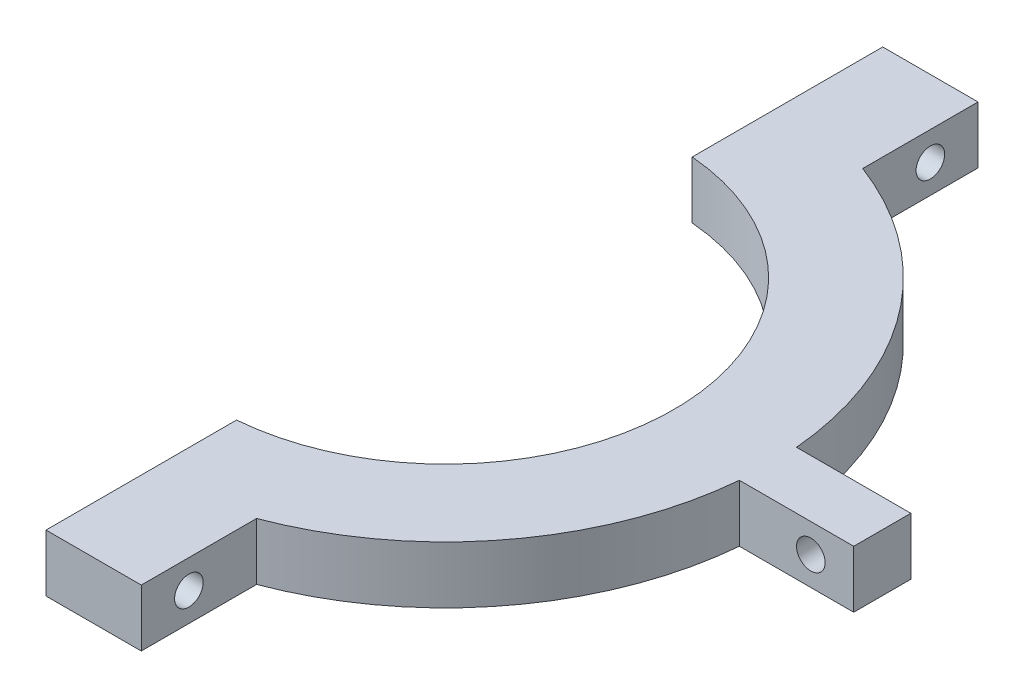
SolidWorks part; units mm, degrees
ref_plane "Front Plane" through (0, 0, 0) normal (0, 0, 1) x (1, 0, 0)
ref_plane "Top Plane" through (0, 0, 0) normal (0, 1, 0) x (1, 0, 0)
ref_plane "Right Plane" through (0, 0, 0) normal (1, 0, 0) x (0, 0, -1)
sketch "Sketch1" plane through (0, 0, 0) normal (0, 1, 0) x (1, 0, 0)
  line L0 (2, 43.9165) -> (2, 23.9165)
  line L1 (2, -23.9165) -> (2, -43.9165)
  line L2 (2, 43.9165) -> (12, 43.9165)
  line L3 (12, 43.9165) -> (12, 31.8119)
  line L4 (2, -43.9165) -> (12, -43.9165)
  line L5 (12, -43.9165) -> (12, -31.8119)
  line L7 (33.8674, -3) -> (45.8674, -3)
  line L9 (33.8674, 3) -> (45.8674, 3)
  line L10 (45.8674, -3) -> (45.8674, 3)
  arc A0 (2, -23.9165) -> (2, 23.9165) centre (0, 0) ccw
  arc A1 (12, -31.8119) -> (33.8674, -3) centre (0, 0) ccw
  arc A2 (33.8674, 3) -> (12, 31.8119) centre (0, 0) ccw
  dimension "D1" = 48
  dimension "D4" = 10
  dimension "D2" = 2
  dimension "D3" = 10
  dimension "D5" = 20
  dimension "D6" = 20
  dimension "D7" = 10
  dimension "D8" = 12
  dimension "D9" = 6
  dimension "D10" = 3
extrude "Boss-Extrude1" add sketch "Sketch1" along normal blind 6
sketch "Sketch3" plane through (0, 0, -3) normal (0, 0, -1) x (-1, 0, 0)
  line L0 (-45.8674, 6) -> (-33.8674, 6) construction
  line L1 (-33.8674, 6) -> (-33.8674, 0) construction
  circle A0 centre (-41.3674, 3) radius 1.5
  dimension "D1" = 3
  dimension "D2" = 3
  dimension "D3" = 7.5
extrude "Cut-Extrude2" cut sketch "Sketch3" against normal through all
sketch "Sketch4" plane through (12, 0, 0) normal (1, 0, 0) x (0, 0, -1)
  line L0 (-43.9165, 6) -> (-31.8119, 6) construction
  line L1 (-43.9165, 6) -> (-43.9165, 0) construction
  circle A0 centre (-38.9165, 3) radius 1.5
  dimension "D1" = 3
  dimension "D2" = 3
  dimension "D3" = 5
extrude "Cut-Extrude3" cut sketch "Sketch4" against normal through all
mirror "Mirror1" about plane through (0, 0, 0) normal (0, 0, 1) of "Cut-Extrude3"
